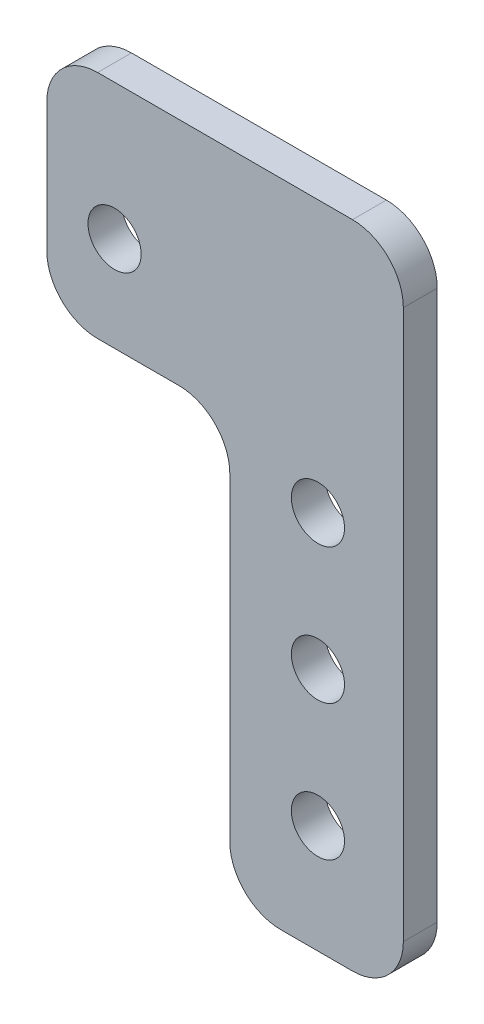
SolidWorks part; units mm, degrees
material "6061-T6 (SS)"
ref_plane "Front Plane" through (0, 0, 0) normal (0, 0, 1) x (1, 0, 0)
ref_plane "Top Plane" through (0, 0, 0) normal (0, 1, 0) x (1, 0, 0)
ref_plane "Right Plane" through (0, 0, 0) normal (1, 0, 0) x (0, 0, -1)
sketch "Sketch1" plane through (0, 0, 0) normal (0, 0, 1) x (1, 0, 0)
  line L6 (28.575, -2.54) -> (61.976, -2.54)
  line L7 (61.976, -2.54) -> (61.976, -63.5)
  line L8 (61.976, -63.5) -> (45.72, -63.5)
  line L9 (45.72, -63.5) -> (45.72, -24.13)
  line L10 (45.72, -24.13) -> (28.575, -24.13)
  line L12 (28.575, -2.54) -> (28.575, -24.13)
  line L18 (0, 0) -> (69.85, 0) construction
  line L19 (0, 0) -> (0, -63.5) construction
  line L20 (0, -63.5) -> (69.85, -63.5) construction
  line L21 (69.85, 0) -> (69.85, -63.5) construction
  circle A0 centre (53.975, -15.24) radius 2.4892 construction
  circle A1 centre (53.975, -27.94) radius 2.4892
  circle A2 centre (53.975, -40.64) radius 2.4892
  circle A3 centre (53.975, -53.34) radius 2.4892
  circle A4 centre (34.925, -15.24) radius 2.4892
  dimension "D4" = 12.7
  dimension "D6" = 4.9784
  dimension "D10" = 24.13
  dimension "D12" = 12.7
  dimension "D13" = 27.051
  dimension "D14" = 6.35
  dimension "D9" = 16.256
  dimension "D11" = 15.875
  dimension "D2" = 63.5
  dimension "D5" = 69.85
  dimension "D7" = 24.13
  dimension "D8" = 2.54
  dimension "D3" = 4
extrude "Boss-Extrude1" add sketch "Sketch1" along normal blind 3.175
fillet "Fillet1" radius 4.7625 6 edges at (61.976, -63.5, 1.5875) (45.72, -63.5, 1.5875) (45.72, -24.13, 1.5875) (28.575, -24.13, 1.5875) (28.575, -2.54, 1.5875) (61.976, -2.54, 1.5875)
